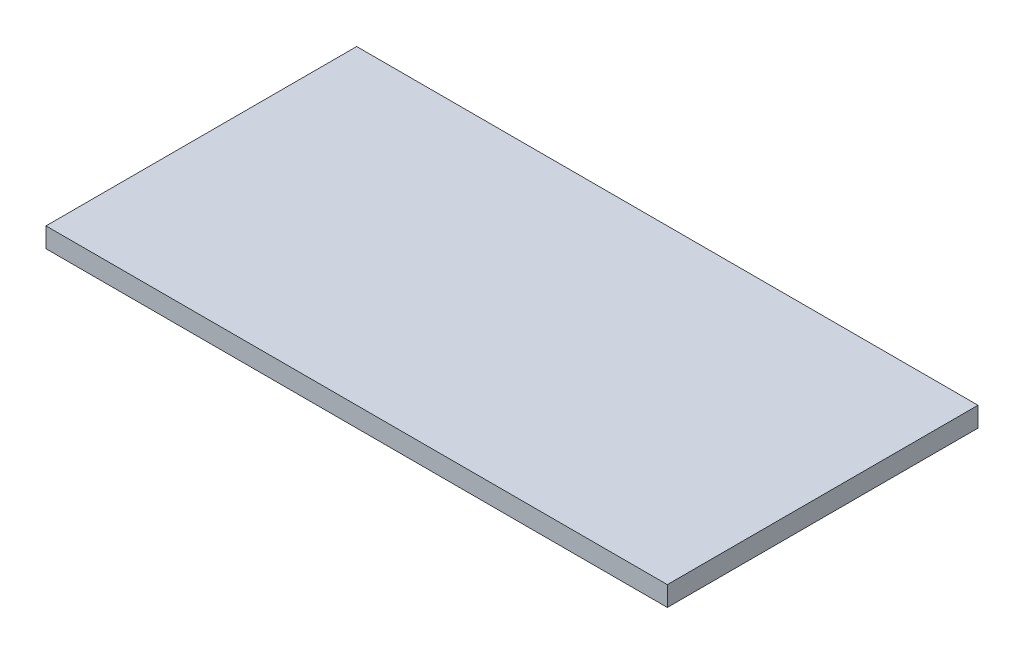
SolidWorks part; units mm, degrees
ref_plane "Спереди" through (0, 0, 0) normal (0, 0, 1) x (1, 0, 0)
ref_plane "Сверху" through (0, 0, 0) normal (0, 1, 0) x (1, 0, 0)
ref_plane "Справа" through (0, 0, 0) normal (1, 0, 0) x (0, 0, -1)
sketch "Эскиз1" plane through (0, 0, 0) normal (0, 1, 0) x (1, 0, 0)
  line L1 (282, -141) -> (-282, -141)
  line L2 (282, -141) -> (282, 141)
  line L3 (282, 141) -> (-282, 141)
  line L4 (-282, -141) -> (-282, 141)
  line L5 (282, -141) -> (-282, 141) construction
  line L6 (282, 141) -> (-282, -141) construction
  point P0 (0, 0)
  dimension "D1" = 564
  dimension "D2" = 282
extrude "Бобышка-Вытянуть1" add sketch "Эскиз1" along normal blind 18
